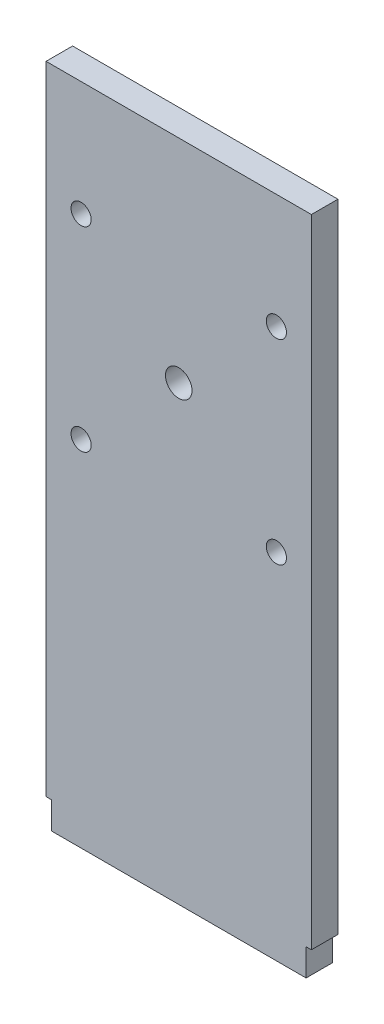
SolidWorks part; units mm, degrees
material "6061 Alloy"
ref_plane "Front Plane" through (0, 0, 0) normal (0, 0, 1) x (1, 0, 0)
ref_plane "Top Plane" through (0, 0, 0) normal (0, 1, 0) x (1, 0, 0)
ref_plane "Right Plane" through (0, 0, 0) normal (1, 0, 0) x (0, 0, -1)
sketch "Sketch2" plane through (0, 0, 0) normal (0, 0, 1) x (1, 0, 0)
  line L0 (31.75, 158.877) -> (31.75, 0) construction
  line L1 (0, 0) -> (63.5, 0)
  line L2 (0, 0) -> (0, 158.877)
  line L3 (0, 158.877) -> (63.5, 158.877)
  line L4 (63.5, 0) -> (63.5, 158.877)
  line L5 (3.556, 131.445) -> (8.382, 131.445) construction
  line L6 (3.556, 136.271) -> (59.944, 136.271) construction
  line L7 (3.556, 136.271) -> (3.556, 79.883) construction
  line L8 (3.556, 79.883) -> (59.944, 79.883) construction
  line L9 (59.944, 136.271) -> (59.944, 79.883) construction
  line L10 (3.556, 136.271) -> (59.944, 79.883) construction
  line L11 (3.556, 79.883) -> (59.944, 136.271) construction
  line L12 (8.382, 131.445) -> (8.382, 136.271) construction
  line L13 (31.75, 108.077) -> (52.1386, 108.077) construction
  circle A0 centre (8.382, 131.445) radius 2.413
  circle A1 centre (55.118, 131.445) radius 2.413
  circle A2 centre (55.118, 84.709) radius 2.413
  circle A3 centre (8.382, 84.709) radius 2.413
  circle A4 centre (31.75, 108.077) radius 3.175
  point P7 (31.75, 108.077)
  dimension "D5" = 4.826
  dimension "D7" = 6.35
  dimension "D1" = 63.5
  dimension "D2" = 108.077
  dimension "D3" = 56.388
  dimension "D4" = 4.826
  dimension "D6" = 50.8
extrude "Boss-Extrude1" add sketch "Sketch2" along normal blind 6.35
sketch "Sketch3" plane through (0, 0, 6.35) normal (0, 0, 1) x (1, 0, 0)
  line L1 (0, 0) -> (1.27, 0)
  line L2 (0, 0) -> (0, 6.477)
  line L3 (0, 6.477) -> (1.27, 6.477)
  line L4 (1.27, 0) -> (1.27, 6.477)
  line L5 (63.5, 0) -> (62.23, 0)
  line L6 (63.5, 0) -> (63.5, 6.477)
  line L7 (63.5, 6.477) -> (62.23, 6.477)
  line L8 (62.23, 0) -> (62.23, 6.477)
  dimension "D1" = 6.477
  dimension "D2" = 60.96
extrude "Cut-Extrude1" cut sketch "Sketch3" against normal through all
equation "\"base length\"= 21"
equation "\"glass pane length\"= 14.125"
equation "\"glass pane width\"= 10.1875"
equation "\"glass pane wall width\"= 3/4"
equation "\"glass lip\"= 1/4"
equation "\"bolt diameter\"= 0.2"
equation "\"stepper body width\"= 2.22"
equation "\"stepper mount offset\"= 0.19"
equation "\"stepper mount diameter\"= 0.19"
equation "\"stepper shaft offset from body\"= 0.79"
equation "\"stepper spacer thickness\"= 0.2"
equation "\"y axis stepper wall height off base\"= 8"
equation "\"y axis stepper wall bracket thickness\"= 1"
equation "\"y axis stepper wall mount side offset\"= 1/2"
equation "\"y axis stepper wall mount top offset\"= 1/2"
equation "\"y axis stepper wall width\"= \"stepper body width\" + 1                  "
equation "\"thin metal\"= 0.12"
equation "\"thick metal\"= 0.25"
equation "\"recognizer width\"= 2.5"
equation "\"recognizer nut plate height\"= 1.25"
equation "\"recognizer nut plate offset\"= 1.5"
equation "\"D1@Sketch2\"=\"recognizer width\""
equation "\"D2@Sketch2\" = \"recognizer arm height to hole\""
equation "\"base width\"= 16.5"
equation "\"recognizer arm height to hole\"= 4.255"
equation "\"recognizer bracket length\"= 4"
equation "\"x axis threaded rod length\"= 3"
